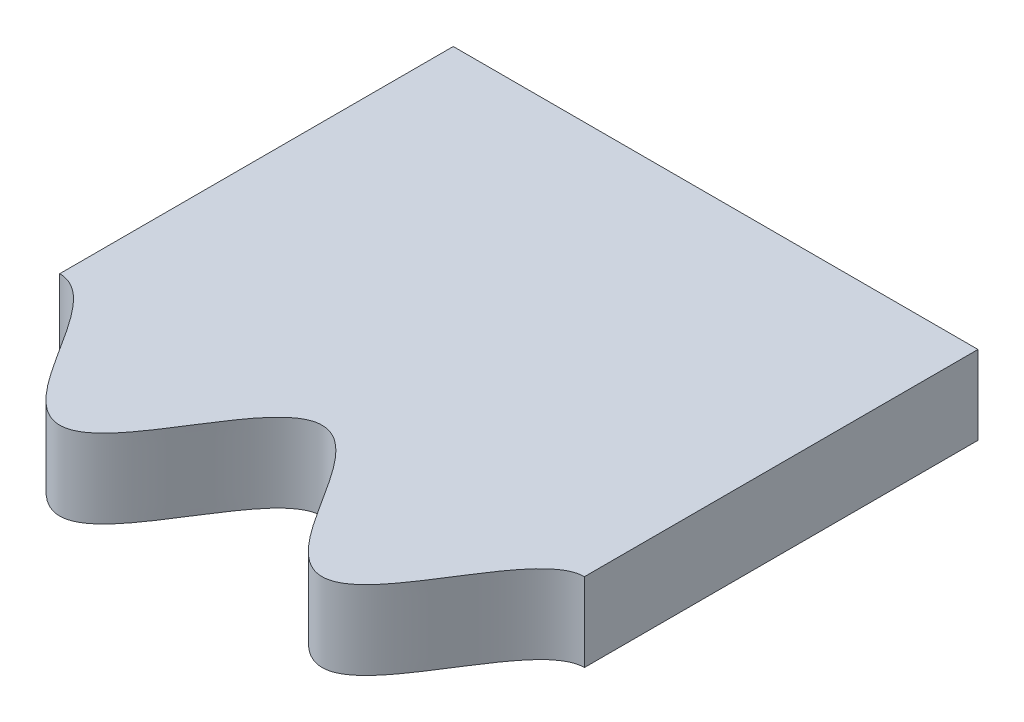
SolidWorks part; units mm, degrees
ref_plane "Front Plane" through (0, 0, 0) normal (0, 0, 1) x (1, 0, 0)
ref_plane "Top Plane" through (0, 0, 0) normal (0, 1, 0) x (1, 0, 0)
ref_plane "Right Plane" through (0, 0, 0) normal (1, 0, 0) x (0, 0, -1)
sketch "Sketch1" plane through (0, 0, 0) normal (0, 1, 0) x (1, 0, 0)
  line L1 (-10, -10) -> (10, -10)
  line L2 (-10, -10) -> (-10, 10)
  line L3 (-10, 10) -> (10, 10)
  line L4 (10, -10) -> (10, 10)
  line L5 (-10, -10) -> (10, 10) construction
  line L6 (-10, 10) -> (10, -10) construction
  point P0 (0, 0)
  dimension "D1" = 20
  dimension "D2" = 20
extrude "Boss-Extrude1" add sketch "Sketch1" along normal blind 3
sketch "Sketch2" plane through (0, 3, 0) normal (0, 1, 0) x (1, 0, 0)
  line L1 (-10, 10) -> (-10, -10) construction
  line L6 (10, -10) -> (10, 10) construction
  line L7 (10, -5) -> (10, -10)
  line L8 (10, -10) -> (-10, -10)
  line L9 (-10, -10) -> (-10, -5)
  spline S0 degree 4 poles (-12, -6.7275) (-11.9654, -6.6757) (-11.8956, -6.5725) (-11.7895, -6.4188) (-11.6438, -6.2167) (-11.4928, -6.0185) (-11.3351, -5.8256) (-11.1688, -5.6399) (-10.9918, -5.4644) (-10.8134, -5.3134) (-10.6529, -5.2028) (-10.5163, -5.1279) (-10.4095, -5.0808) (-10.3218, -5.0493) (-10.2423, -5.0278) (-10.1753, -5.0142) (-10.1162, -5.0062) (-10.0655, -5.002) (-10.0182, -4.9999) (-9.9842, -4.9998) (-9.9394, -5.0017) (-9.892, -5.0055) (-9.8359, -5.0124) (-9.773, -5.0243) (-9.6989, -5.0432) (-9.616, -5.071) (-9.5154, -5.1128) (-9.3873, -5.1789) (-9.2371, -5.2764) (-9.07, -5.4098) (-8.9046, -5.5651) (-8.749, -5.7301) (-8.6013, -5.9021) (-8.4601, -6.0795) (-8.324, -6.2608) (-8.1827, -6.4585) (-8.0359, -6.6724) (-7.8835, -6.9022) (-7.7248, -7.1474) (-7.5284, -7.4551) (-7.2936, -7.825) (-7.0346, -8.2261) (-6.743, -8.6525) (-6.4528, -9.0386) (-6.1598, -9.3795) (-5.8517, -9.6694) (-5.521, -9.8895) (-5.1672, -10.0108) (-4.8167, -10.0082) (-4.4632, -9.8815) (-4.1325, -9.6563) (-3.8252, -9.3634) (-3.5336, -9.0214) (-3.2446, -8.635) (-2.9542, -8.2091) (-2.6569, -7.748) (-2.3458, -7.2563) (-2.0486, -6.7951) (-1.7583, -6.3691) (-1.4695, -5.9825) (-1.1782, -5.6403) (-0.8714, -5.3469) (-0.5412, -5.1209) (-0.1883, -4.9928) (0.1621, -4.9883) (0.5165, -5.1081) (0.8478, -5.3274) (1.1563, -5.6169) (1.4496, -5.9574) (1.7401, -6.3434) (2.0319, -6.7697) (2.4096, -7.3549) (2.7809, -7.9452) (3.1457, -8.5013) (3.5233, -9.0086) (3.8169, -9.3546) (4.126, -9.6513) (4.459, -9.8796) (4.8145, -10.0081) (5.1665, -10.011) (5.521, -9.8895) (5.8517, -9.6694) (6.1598, -9.3794) (6.4528, -9.0387) (6.743, -8.6525) (7.0346, -8.2261) (7.3332, -7.7637) (7.6064, -7.3317) (7.8431, -6.963) (8.0359, -6.6724) (8.1827, -6.4585) (8.324, -6.2608) (8.4601, -6.0795) (8.6013, -5.9021) (8.749, -5.7301) (8.9046, -5.5651) (9.07, -5.4098) (9.2371, -5.2764) (9.4057, -5.167) (9.5545, -5.0935) (9.6777, -5.0486) (9.773, -5.0243) (9.8359, -5.0124) (9.892, -5.0055) (9.9394, -5.0017) (9.9842, -4.9998) (10.0182, -4.9999) (10.0655, -5.002) (10.1162, -5.0062) (10.1753, -5.0142) (10.2423, -5.0278) (10.3218, -5.0493) (10.4095, -5.0808) (10.5163, -5.1279) (10.6529, -5.2028) (10.8134, -5.3134) (10.9918, -5.4644) (11.1467, -5.618) (11.2727, -5.756) (11.374, -5.8743) (11.4529, -5.9706) (11.5494, -6.0928) (11.662, -6.2419) (11.7895, -6.4188) (11.8956, -6.5725) (11.9654, -6.6757) (12, -6.7275) knots 0 0 0 0 0 0.007168 0.014336 0.021504 0.028672 0.03584 0.043008 0.050176 0.057345 0.062712 0.065396 0.06808 0.070764 0.073448 0.07479 0.076132 0.077474 0.078815 0.08007 0.081324 0.082579 0.083833 0.086342 0.08885 0.091359 0.093868 0.098885 0.105408 0.111931 0.118454 0.124976 0.131499 0.138022 0.144545 0.151068 0.159472 0.167876 0.176281 0.184685 0.201494 0.218303 0.231224 0.244144 0.257065 0.269985 0.279769 0.289552 0.299506 0.309461 0.322382 0.335304 0.348225 0.361147 0.377889 0.394632 0.411374 0.428117 0.441039 0.45396 0.466882 0.479803 0.489758 0.499712 0.509495 0.519278 0.532199 0.54512 0.55804 0.570961 0.587769 0.604578 0.638196 0.651242 0.664287 0.677333 0.690379 0.700413 0.710448 0.720231 0.730015 0.742935 0.755856 0.768776 0.781697 0.798506 0.815315 0.832124 0.840528 0.848932 0.855455 0.861978 0.868501 0.875024 0.881546 0.888069 0.894592 0.901115 0.906132 0.91115 0.913658 0.916167 0.917421 0.918676 0.91993 0.921185 0.922526 0.923868 0.92521 0.926552 0.929236 0.93192 0.934604 0.937288 0.942655 0.949824 0.956992 0.96416 0.967744 0.971328 0.974912 0.978496 0.985664 0.992832 1 1 1 1 1 construction
  spline S1 degree 4 poles (-10, -5) (-9.9908, -5) (-9.9724, -5.0003) (-9.9394, -5.0017) (-9.892, -5.0055) (-9.8359, -5.0124) (-9.773, -5.0243) (-9.6989, -5.0432) (-9.616, -5.071) (-9.5154, -5.1128) (-9.3873, -5.1789) (-9.2371, -5.2764) (-9.07, -5.4098) (-8.9046, -5.5651) (-8.749, -5.7301) (-8.6013, -5.9021) (-8.4601, -6.0795) (-8.324, -6.2608) (-8.1827, -6.4585) (-8.0359, -6.6724) (-7.8835, -6.9022) (-7.7248, -7.1474) (-7.5284, -7.4551) (-7.2936, -7.825) (-7.0346, -8.2261) (-6.743, -8.6525) (-6.4528, -9.0386) (-6.1598, -9.3795) (-5.8517, -9.6694) (-5.521, -9.8895) (-5.1672, -10.0108) (-4.8167, -10.0082) (-4.4632, -9.8815) (-4.1325, -9.6563) (-3.8252, -9.3634) (-3.5336, -9.0214) (-3.2446, -8.635) (-2.9542, -8.2091) (-2.6569, -7.748) (-2.3458, -7.2563) (-2.0486, -6.7951) (-1.7583, -6.3691) (-1.4695, -5.9825) (-1.1782, -5.6403) (-0.8714, -5.3469) (-0.5412, -5.1209) (-0.1883, -4.9928) (0.1621, -4.9883) (0.5165, -5.1081) (0.8478, -5.3274) (1.1563, -5.6169) (1.4496, -5.9574) (1.7401, -6.3434) (2.0319, -6.7697) (2.4096, -7.3549) (2.7809, -7.9452) (3.1457, -8.5013) (3.5233, -9.0086) (3.8169, -9.3546) (4.126, -9.6513) (4.459, -9.8796) (4.8145, -10.0081) (5.1665, -10.011) (5.521, -9.8895) (5.8517, -9.6694) (6.1598, -9.3794) (6.4528, -9.0387) (6.743, -8.6525) (7.0346, -8.2261) (7.3332, -7.7637) (7.6064, -7.3317) (7.8431, -6.963) (8.0359, -6.6724) (8.1827, -6.4585) (8.324, -6.2608) (8.4601, -6.0795) (8.6013, -5.9021) (8.749, -5.7301) (8.9046, -5.5651) (9.07, -5.4098) (9.2371, -5.2764) (9.4057, -5.167) (9.5545, -5.0935) (9.6777, -5.0486) (9.773, -5.0243) (9.8359, -5.0124) (9.892, -5.0055) (9.9394, -5.0017) (9.9724, -5.0003) (9.9908, -5) (10, -5) knots 0.078815 0.078815 0.078815 0.078815 0.078815 0.08007 0.081324 0.082579 0.083833 0.086342 0.08885 0.091359 0.093868 0.098885 0.105408 0.111931 0.118454 0.124976 0.131499 0.138022 0.144545 0.151068 0.159472 0.167876 0.176281 0.184685 0.201494 0.218303 0.231224 0.244144 0.257065 0.269985 0.279769 0.289552 0.299506 0.309461 0.322382 0.335304 0.348225 0.361147 0.377889 0.394632 0.411374 0.428117 0.441039 0.45396 0.466882 0.479803 0.489758 0.499712 0.509495 0.519278 0.532199 0.54512 0.55804 0.570961 0.587769 0.604578 0.638196 0.651242 0.664287 0.677333 0.690379 0.700413 0.710448 0.720231 0.730015 0.742935 0.755856 0.768776 0.781697 0.798506 0.815315 0.832124 0.840528 0.848932 0.855455 0.861978 0.868501 0.875024 0.881546 0.888069 0.894592 0.901115 0.906132 0.91115 0.913658 0.916167 0.917421 0.918676 0.91993 0.921185 0.921185 0.921185 0.921185 0.921185
  point P1 (-19.809, 3.2113)
  point P8 (0, 0)
  line M1 (10, -10) -> (10, 10)
  line M3 (-10, 10) -> (-10, -10)
  line M4 (-10, -10) -> (10, -10)
  dimension "D3" = 5
extrude "Cut-Extrude1" cut sketch "Sketch2" against normal through all both and the other way through all contours S1 M3 M4 M1
